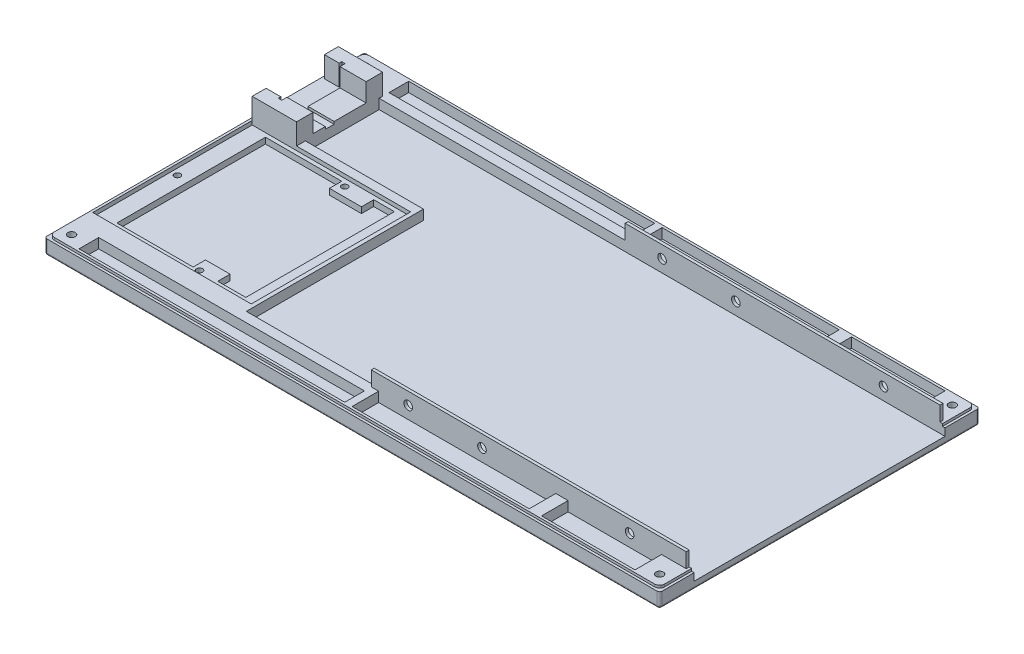
SolidWorks part; units mm, degrees
ref_plane "Front Plane" through (0, 0, 0) normal (0, 0, 1) x (1, 0, 0)
ref_plane "Top Plane" through (0, 0, 0) normal (0, 1, 0) x (1, 0, 0)
ref_plane "Right Plane" through (0, 0, 0) normal (1, 0, 0) x (0, 0, -1)
sketch "Sketch1" plane through (0, 0, 0) normal (0, 1, 0) x (1, 0, 0)
  line L1 (-125, -65) -> (125, -65)
  line L2 (-125, -65) -> (-125, 65)
  line L3 (-125, 65) -> (125, 65)
  line L4 (125, -65) -> (125, 65)
  line L5 (-125, -65) -> (125, 65) construction
  line L6 (-125, 65) -> (125, -65) construction
  point P0 (0, 0)
extrude "Boss-Extrude1" add sketch "Sketch1" along normal blind 3
sketch "Sketch2" plane through (0, 0, 0) normal (0, 1, 0) x (1, 0, 0)
  line L0 (125, -65) -> (125, 65) construction
  line L1 (-125, 65) -> (125, 65)
  line L2 (-125, 65) -> (-125, 64)
  line L3 (-125, 64) -> (125, 64)
  line L4 (125, 65) -> (125, 64)
  dimension "D1" = 1
extrude "Boss-Extrude2" add sketch "Sketch2" along normal blind 6
sketch "Sketch3" plane through (0, 3, 0) normal (0, 1, 0) x (1, 0, 0)
  line L0 (125, -65) -> (125, 64) construction
  line L1 (-125, -65) -> (125, -65)
  line L2 (-125, -65) -> (-125, -64)
  line L3 (-125, -64) -> (125, -64)
  line L4 (125, -65) -> (125, -64)
  dimension "D1" = 1
extrude "Boss-Extrude3" add sketch "Sketch3" along normal blind 3
sketch "Sketch4" plane through (0, 3, 0) normal (0, 1, 0) x (1, 0, 0)
  line L0 (125, -64) -> (-125, -64) construction
  line L1 (-125, 64) -> (-124, 64)
  line L2 (-125, 64) -> (-125, -64)
  line L3 (-125, -64) -> (-124, -64)
  line L4 (-124, 64) -> (-124, -64)
  dimension "D1" = 1
extrude "Boss-Extrude4" add sketch "Sketch4" along normal blind 3
sketch "Sketch6" plane through (0, 3, 0) normal (0, 1, 0) x (1, 0, 0)
  line L1 (125, -65) -> (124, -65)
  line L2 (125, -65) -> (125, -51)
  line L3 (125, -51) -> (124, -51)
  line L4 (124, -65) -> (124, -51)
  dimension "D1" = 1
  dimension "D2" = 14
extrude "Boss-Extrude5" add sketch "Sketch6" along normal blind 3
sketch "Sketch7" plane through (0, 3, 0) normal (0, 1, 0) x (1, 0, 0)
  line L1 (125, 65) -> (124, 65)
  line L2 (125, 65) -> (125, 51)
  line L3 (125, 51) -> (124, 51)
  line L4 (124, 65) -> (124, 51)
  dimension "D1" = 1
  dimension "D2" = 14
extrude "Boss-Extrude6" add sketch "Sketch7" along normal blind 3
sketch "Sketch8" plane through (0, 3, 0) normal (0, 1, 0) x (1, 0, 0)
  line L0 (-124, 64) -> (124, 64) construction
  line L1 (124, 51) -> (123, 51)
  line L2 (124, 51) -> (124, 64)
  line L3 (124, 64) -> (123, 64)
  line L4 (123, 51) -> (123, 64)
  dimension "D1" = 1
extrude "Boss-Extrude7" add sketch "Sketch8" along normal blind 4
sketch "Sketch10" plane through (0, 3, 0) normal (0, 1, 0) x (1, 0, 0)
  line L0 (-124, -64) -> (-124, 64) construction
  line L1 (123, 64) -> (-124, 64)
  line L2 (123, 64) -> (123, 63)
  line L3 (123, 63) -> (-124, 63)
  line L4 (-124, 64) -> (-124, 63)
  dimension "D1" = 1
extrude "Boss-Extrude8" add sketch "Sketch10" along normal blind 4
sketch "Sketch11" plane through (0, 3, 0) normal (0, 1, 0) x (1, 0, 0)
  line L0 (124, -64) -> (-124, -64) construction
  line L1 (-124, 63) -> (-123, 63)
  line L2 (-124, 63) -> (-124, -64)
  line L3 (-124, -64) -> (-123, -64)
  line L4 (-123, 63) -> (-123, -64)
  dimension "D1" = 1
extrude "Boss-Extrude9" add sketch "Sketch11" along normal blind 4
sketch "Sketch14" plane through (0, 3, 0) normal (0, 1, 0) x (1, 0, 0)
  line L0 (124, -51) -> (124, -64) construction
  line L1 (-123, -64) -> (124, -64)
  line L2 (-123, -64) -> (-123, -63)
  line L3 (-123, -63) -> (124, -63)
  line L4 (124, -64) -> (124, -63)
  dimension "D1" = 1
extrude "Boss-Extrude10" add sketch "Sketch14" along normal blind 4
sketch "Sketch15" plane through (0, 3, 0) normal (0, 1, 0) x (1, 0, 0)
  line L1 (124, -63) -> (123, -63)
  line L2 (124, -63) -> (124, -51)
  line L3 (124, -51) -> (123, -51)
  line L4 (123, -63) -> (123, -51)
  dimension "D1" = 1
extrude "Boss-Extrude11" add sketch "Sketch15" along normal blind 4
fillet "Fillet1" radius 1 8 edges at (0, 0, -65) (-125, 3, -65) (-125, 0, 0) (-125, 3, 65) (125, 3, -65) (125, 3, 65) (0, 0, 65) (125, 0, 0)
sketch "Sketch17" plane through (0, 3, 0) normal (0, 1, 0) x (1, 0, 0)
  line L1 (123, 51) -> (-5, 51)
  line L2 (123, 51) -> (123, 52.2)
  line L3 (123, 52.2) -> (-5, 52.2)
  line L4 (-5, 51) -> (-5, 52.2)
  dimension "D1" = 1.2
  dimension "D2" = 128
extrude "Boss-Extrude12" add sketch "Sketch17" along normal blind 10
sketch "Sketch19" plane through (0, 3, 0) normal (0, 1, 0) x (1, 0, 0)
  line L1 (123, -51) -> (-5, -51)
  line L2 (123, -51) -> (123, -52.2)
  line L3 (123, -52.2) -> (-5, -52.2)
  line L4 (-5, -51) -> (-5, -52.2)
  dimension "D1" = 1.2
  dimension "D2" = 128
extrude "Boss-Extrude13" add sketch "Sketch19" along normal blind 10
sketch "Sketch22" plane through (0, 3, 0) normal (0, 1, 0) x (1, 0, 0)
  line L0 (123, -63) -> (-123, -63) construction
  line L1 (-5, -52.2) -> (-2, -52.2)
  line L2 (-5, -52.2) -> (-5, -63)
  line L3 (-5, -63) -> (-2, -63)
  line L4 (-2, -52.2) -> (-2, -63)
  dimension "D1" = 3
extrude "Boss-Extrude14" add sketch "Sketch22" along normal blind 4
sketch "Sketch24" plane through (0, 3, 0) normal (0, 1, 0) x (1, 0, 0)
  line L0 (-123, 63) -> (123, 63) construction
  line L1 (-5, 52.2) -> (-2, 52.2)
  line L2 (-5, 52.2) -> (-5, 63)
  line L3 (-5, 63) -> (-2, 63)
  line L4 (-2, 52.2) -> (-2, 63)
  dimension "D1" = 3
extrude "Boss-Extrude15" add sketch "Sketch24" along normal blind 4
sketch "Sketch25" plane through (0, 0, -51) normal (0, 0, 1) x (1, 0, 0)
  circle A0 centre (100, 8) radius 1.75
  dimension "D1" = 5
  dimension "D2" = 25
extrude "FloppyMountHole001" cut sketch "Sketch25" against normal up to next
sketch "Sketch26" plane through (0, 0, -51) normal (0, 0, 1) x (1, 0, 0)
  line L0 (-5, 13) -> (123, 13) construction
  circle A0 centre (40, 8) radius 1.75
  dimension "D1" = 5
  dimension "D2" = 85
extrude "FloppyMountHole002" cut sketch "Sketch26" against normal up to next
sketch "Sketch27" plane through (0, 0, -51) normal (0, 0, 1) x (1, 0, 0)
  circle A0 centre (10, 8) radius 1.75
  dimension "D1" = 115
  dimension "D2" = 5
extrude "FloppyMountHole003" cut sketch "Sketch27" against normal up to next
sketch "Sketch28" plane through (0, 0, 52.2) normal (0, 0, 1) x (1, 0, 0)
  circle A0 centre (100, 8) radius 1.75
  dimension "D1" = 5
  dimension "D2" = 25
extrude "FloppyMountHole004" cut sketch "Sketch28" against normal up to next
sketch "Sketch29" plane through (0, 0, 52.2) normal (0, 0, 1) x (1, 0, 0)
  circle A0 centre (40, 8) radius 1.75
  dimension "D1" = 5
  dimension "D2" = 85
extrude "FloppyMountHole005" cut sketch "Sketch29" against normal up to next
sketch "Sketch30" plane through (0, 0, 52.2) normal (0, 0, 1) x (1, 0, 0)
  circle A0 centre (10, 8) radius 1.75
  dimension "D1" = 5
  dimension "D2" = 115
extrude "FloppyMountHole006" cut sketch "Sketch30" against normal up to next
sketch "Sketch31" plane through (0, 3, 0) normal (0, 1, 0) x (1, 0, 0)
  line L0 (123, -63) -> (-2, -63) construction
  line L1 (75, -63) -> (70, -63)
  line L2 (75, -63) -> (75, -52.2)
  line L3 (75, -52.2) -> (70, -52.2)
  line L4 (70, -63) -> (70, -52.2)
  line L5 (-5, -52.2) -> (123, -52.2) construction
  dimension "D1" = 5
  dimension "D2" = 48
extrude "Boss-Extrude16" add sketch "Sketch31" along normal blind 4
sketch "Sketch33" plane through (0, 3, 0) normal (0, 1, 0) x (1, 0, 0)
  line L0 (-2, 63) -> (123, 63) construction
  line L1 (75, 63) -> (70, 63)
  line L2 (75, 63) -> (75, 52.2)
  line L3 (75, 52.2) -> (70, 52.2)
  line L4 (70, 63) -> (70, 52.2)
  line L5 (123, 52.2) -> (-2, 52.2) construction
  dimension "D1" = 5
  dimension "D2" = 48
extrude "Boss-Extrude18" add sketch "Sketch33" along normal blind 4
fillet "Fillet2" radius 2 4 edges at (-124, 6.5, -64) (-124, 6.5, 64) (124, 6.5, 64) (124, 6.5, -64)
sketch "Sketch35" plane through (0, 3, 0) normal (0, 1, 0) x (1, 0, 0)
  line L0 (-123, -63) -> (-123, 63) construction
  line L1 (-57, -51) -> (-123, -51)
  line L2 (-57, -51) -> (-57, -47.4)
  line L3 (-57, -47.4) -> (-123, -47.4)
  line L4 (-123, -51) -> (-123, -47.4)
  dimension "D1" = 66
  dimension "D2" = 3.6
extrude "GWOuter001" add sketch "Sketch35" along normal blind 4
sketch "Sketch36" plane through (0, 3, 0) normal (0, 1, 0) x (1, 0, 0)
  line L1 (-57, -47.4) -> (-58.6, -47.4)
  line L2 (-57, -47.4) -> (-57, 17.4)
  line L3 (-57, 17.4) -> (-58.6, 17.4)
  line L4 (-58.6, -47.4) -> (-58.6, 17.4)
  dimension "D1" = 1.6
  dimension "D2" = 64.8
extrude "GWOuter002" add sketch "Sketch36" along normal blind 4
sketch "Sketch37" plane through (0, 3, 0) normal (0, 1, 0) x (1, 0, 0)
  line L0 (-123, -47.4) -> (-123, 63) construction
  line L1 (-57, 17.4) -> (-123, 17.4)
  line L2 (-57, 17.4) -> (-57, 21)
  line L3 (-57, 21) -> (-123, 21)
  line L4 (-123, 17.4) -> (-123, 21)
  dimension "D1" = 3.6
extrude "GWOuter003" add sketch "Sketch37" along normal blind 4
sketch "Sketch38" plane through (0, 3, 0) normal (0, 1, 0) x (1, 0, 0)
  line L0 (-58.6, -47.4) -> (-123, -47.4) construction
  line L1 (-123, 17.4) -> (-116, 17.4)
  line L2 (-123, 17.4) -> (-123, -47.4)
  line L3 (-123, -47.4) -> (-116, -47.4)
  line L4 (-116, 17.4) -> (-116, -47.4)
  dimension "D1" = 7
extrude "GWSupportBack" add sketch "Sketch38" along normal blind 2.4
sketch "Sketch39" plane through (0, 3, 0) normal (0, 1, 0) x (1, 0, 0)
  line L0 (-58.6, -47.4) -> (-116, -47.4) construction
  line L1 (-58.6, 17.4) -> (-63.6, 17.4)
  line L2 (-58.6, 17.4) -> (-58.6, -47.4)
  line L3 (-58.6, -47.4) -> (-63.6, -47.4)
  line L4 (-63.6, 17.4) -> (-63.6, -47.4)
  dimension "D1" = 5
extrude "GWSupportFrt" add sketch "Sketch39" along normal blind 2.4
sketch "Sketch40" plane through (0, 3, 0) normal (0, 1, 0) x (1, 0, 0)
  line L0 (-63.6, 17.4) -> (-63.6, -47.4) construction
  line L1 (-116, 17.4) -> (-63.6, 17.4)
  line L2 (-116, 17.4) -> (-116, 15.8)
  line L3 (-116, 15.8) -> (-63.6, 15.8)
  line L4 (-63.6, 17.4) -> (-63.6, 15.8)
  dimension "D1" = 1.6
extrude "GWSupportLt" add sketch "Sketch40" along normal blind 2.4
sketch "Sketch41" plane through (0, 3, 0) normal (0, 1, 0) x (1, 0, 0)
  line L0 (-63.6, 15.8) -> (-63.6, -47.4) construction
  line L1 (-116, -47.4) -> (-63.6, -47.4)
  line L2 (-116, -47.4) -> (-116, -44.6)
  line L3 (-116, -44.6) -> (-63.6, -44.6)
  line L4 (-63.6, -47.4) -> (-63.6, -44.6)
  dimension "D1" = 2.8
extrude "GWSupportRt" add sketch "Sketch41" along normal blind 2.4
sketch "Sketch43" plane through (0, 3, 0) normal (0, 1, 0) x (1, 0, 0)
  line L0 (-63.6, -44.6) -> (-116, -44.6) construction
  line L1 (-75, -39.6) -> (-85, -39.6)
  line L2 (-75, -39.6) -> (-75, -44.6)
  line L3 (-75, -44.6) -> (-85, -44.6)
  line L4 (-85, -39.6) -> (-85, -44.6)
  dimension "D1" = 11.4
  dimension "D2" = 10
  dimension "D3" = 5
extrude "GWScrewRt" add sketch "Sketch43" along normal blind 2.4
sketch "Sketch44" plane through (0, 3, 0) normal (0, 1, 0) x (1, 0, 0)
  line L0 (-123, -63) -> (-123, -51) construction
  line L1 (-5, -51) -> (-123, -51)
  line L2 (-5, -51) -> (-5, -55)
  line L3 (-5, -55) -> (-123, -55)
  line L4 (-123, -51) -> (-123, -55)
  dimension "D1" = 4
extrude "Boss-Extrude28" add sketch "Sketch44" along normal blind 4
sketch "Sketch45" plane through (0, 3, 0) normal (0, 1, 0) x (1, 0, 0)
  line L0 (-57, 21) -> (-123, 21) construction
  line L1 (-123, 63) -> (-105, 63)
  line L2 (-123, 63) -> (-123, 21)
  line L3 (-123, 21) -> (-105, 21)
  line L4 (-105, 63) -> (-105, 21)
  line L5 (-125, 64) -> (-125, -64) construction
  dimension "D1" = 20
extrude "Boss-Extrude29" add sketch "Sketch45" along normal blind 4
sketch "Sketch46" plane through (0, 3, 0) normal (0, 1, 0) x (1, 0, 0)
  line L0 (-5, -63) -> (-123, -63) construction
  line L1 (-123, -55) -> (-113, -55)
  line L2 (-123, -55) -> (-123, -63)
  line L3 (-123, -63) -> (-113, -63)
  line L4 (-113, -55) -> (-113, -63)
  dimension "D1" = 10
extrude "Boss-Extrude30" add sketch "Sketch46" along normal blind 4
sketch "Sketch47" plane through (0, 3, 0) normal (0, 1, 0) x (1, 0, 0)
  line L0 (123, 52.2) -> (75, 52.2) construction
  line L1 (123, 63) -> (113, 63)
  line L2 (123, 63) -> (123, 52.2)
  line L3 (123, 52.2) -> (113, 52.2)
  line L4 (113, 63) -> (113, 52.2)
  dimension "D1" = 10
extrude "Boss-Extrude31" add sketch "Sketch47" along normal blind 4
sketch "Sketch48" plane through (0, 3, 0) normal (0, 1, 0) x (1, 0, 0)
  line L0 (75, -52.2) -> (123, -52.2) construction
  line L1 (123, -63) -> (113, -63)
  line L2 (123, -63) -> (123, -52.2)
  line L3 (123, -52.2) -> (113, -52.2)
  line L4 (113, -63) -> (113, -52.2)
  dimension "D1" = 10
extrude "Boss-Extrude32" add sketch "Sketch48" along normal blind 4
sketch "Sketch49" plane through (0, 3, 0) normal (0, 1, 0) x (1, 0, 0)
  line L0 (-105, 21) -> (-105, 63) construction
  line L1 (-5, 51) -> (-105, 51)
  line L2 (-5, 51) -> (-5, 55)
  line L3 (-5, 55) -> (-105, 55)
  line L4 (-105, 51) -> (-105, 55)
  dimension "D1" = 4
extrude "Boss-Extrude33" add sketch "Sketch49" along normal blind 4
sketch "Sketch50" plane through (0, 3, 0) normal (0, 1, 0) x (1, 0, 0)
  line L0 (-116, 15.8) -> (-63.6, 15.8) construction
  line L2 (-72, 15.8) -> (-85, 15.8)
  line L3 (-72, 15.8) -> (-72, 10.8)
  line L4 (-72, 10.8) -> (-85, 10.8)
  line L5 (-85, 15.8) -> (-85, 10.8)
  dimension "D1" = 8.4
  dimension "D2" = 13
  dimension "D3" = 5
extrude "GWScrewLt" add sketch "Sketch50" along normal blind 2.4
sketch "Sketch51" plane through (0, 5.4, 0) normal (0, 1, 0) x (1, 0, 0)
  circle A0 centre (-82.5, 14.5) radius 1.25
  dimension "D1" = 40.5
  dimension "D2" = 2.9
extrude "GWLSideMountHole" cut sketch "Sketch51" against normal offset from surface (5 mm away) 5
sketch "Sketch52" plane through (0, 5.4, 0) normal (0, 1, 0) x (1, 0, 0)
  line L0 (-123, 17.4) -> (-123, -47.4) construction
  circle A0 centre (-82.5, -44.5) radius 1.25
  dimension "D1" = 40.5
  dimension "D2" = 2.9
extrude "GWRSideMountHole" cut sketch "Sketch52" against normal offset from surface (5 mm away) 5
sketch "Sketch53" plane through (0, 5.4, 0) normal (0, 1, 0) x (1, 0, 0)
  circle A0 centre (-120.5, -15.5) radius 1.25
  dimension "D1" = 31.9
  dimension "D2" = 2.5
extrude "GWBackMountHole" cut sketch "Sketch53" against normal offset from surface (5 mm away) 5
sketch "Sketch54" plane through (0, 7, 0) normal (0, 1, 0) x (1, 0, 0)
  line L6 (-123, 17.4) -> (-117, 17.4)
  line L7 (-123, 17.4) -> (-123, 23.05)
  line L8 (-123, 23.05) -> (-117, 23.05)
  line L9 (-117, 17.4) -> (-117, 23.05)
  dimension "D1" = 5.65
  dimension "D2" = 6
extrude "Molex001" add sketch "Sketch54" along normal blind 8.5
sketch "Sketch55" plane through (0, 7, 0) normal (0, 1, 0) x (1, 0, 0)
  line L1 (-123, 52.4) -> (-117, 52.4)
  line L2 (-123, 52.4) -> (-123, 46.75)
  line L3 (-123, 46.75) -> (-117, 46.75)
  line L4 (-117, 52.4) -> (-117, 46.75)
  line L5 (-125, 64) -> (-125, -64) construction
  dimension "D1" = 23.7
  dimension "D2" = 5.65
  dimension "D3" = 8
  dimension "D4" = 2
extrude "Molex002" add sketch "Sketch55" along normal blind 8.5
sketch "Sketch56" plane through (0, 7, 0) normal (0, 1, 0) x (1, 0, 0)
  line L5 (-117, 17.4) -> (-115.6, 17.4)
  line L6 (-117, 17.4) -> (-117, 22)
  line L7 (-117, 22) -> (-115.6, 22)
  line L8 (-115.6, 17.4) -> (-115.6, 22)
  dimension "D1" = 4.6
  dimension "D2" = 1.4
extrude "Molex003" add sketch "Sketch56" along normal blind 8.5
sketch "Sketch57" plane through (0, 7, 0) normal (0, 1, 0) x (1, 0, 0)
  line L1 (-117, 52.4) -> (-115.6, 52.4)
  line L2 (-117, 52.4) -> (-117, 47.8)
  line L3 (-117, 47.8) -> (-115.6, 47.8)
  line L4 (-115.6, 52.4) -> (-115.6, 47.8)
  dimension "D1" = 1.4
  dimension "D2" = 4.6
extrude "Molex004" add sketch "Sketch57" along normal blind 8.5
sketch "Sketch58" plane through (0, 7, 0) normal (0, 1, 0) x (1, 0, 0)
  line L0 (-105, 21) -> (-105, 51) construction
  line L1 (-115.6, 52.4) -> (-105, 52.4)
  line L2 (-115.6, 52.4) -> (-115.6, 45.7)
  line L3 (-115.6, 45.7) -> (-105, 45.7)
  line L4 (-105, 52.4) -> (-105, 45.7)
  dimension "D1" = 6.7
extrude "Molex005" add sketch "Sketch58" along normal blind 8.5
sketch "Sketch59" plane through (0, 7, 0) normal (0, 1, 0) x (1, 0, 0)
  line L0 (-105, 21) -> (-105, 45.7) construction
  line L1 (-115.6, 17.4) -> (-105, 17.4)
  line L2 (-115.6, 17.4) -> (-115.6, 24.1)
  line L3 (-115.6, 24.1) -> (-105, 24.1)
  line L4 (-105, 17.4) -> (-105, 24.1)
  dimension "D1" = 6.7
extrude "Molex006" add sketch "Sketch59" along normal blind 8.5
sketch "Sketch60" plane through (0, 7, 0) normal (0, 1, 0) x (1, 0, 0)
  line L0 (-105, 24.1) -> (-105, 45.7) construction
  line L1 (-115.6, 45.7) -> (-105, 45.7)
  line L2 (-115.6, 45.7) -> (-115.6, 32.7)
  line L3 (-115.6, 32.7) -> (-105, 32.7)
  line L4 (-105, 45.7) -> (-105, 32.7)
  dimension "D1" = 13
extrude "Molex007" add sketch "Sketch60" along normal blind 1
sketch "Sketch61" plane through (0, 7, 0) normal (0, 1, 0) x (1, 0, 0)
  line L0 (-105, 24.1) -> (-105, 32.7) construction
  line L1 (-115.6, 24.1) -> (-105, 24.1)
  line L2 (-115.6, 24.1) -> (-115.6, 29.1)
  line L3 (-115.6, 29.1) -> (-105, 29.1)
  line L4 (-105, 24.1) -> (-105, 29.1)
  dimension "D1" = 5
extrude "Molex008" add sketch "Sketch61" along normal blind 1
sketch "Sketch62" plane through (0, 7, 0) normal (0, 1, 0) x (1, 0, 0)
  line L0 (124, 65) -> (-124, 65) construction
  line L1 (-125, 64) -> (-125, -64) construction
  circle A0 centre (-119.5, 59.5) radius 1.5
  dimension "D1" = 5.5
  dimension "D2" = 5.5
extrude "CaseMuntHole001" cut sketch "Sketch62" against normal through all
sketch "Sketch63" plane through (0, 7, 0) normal (0, 1, 0) x (1, 0, 0)
  line L0 (125, 51) -> (125, 64) construction
  line L1 (124, 65) -> (-124, 65) construction
  circle A0 centre (119.5, 59.5) radius 1.5
  dimension "D1" = 5.5
  dimension "D2" = 5.5
extrude "CaseMuntHole002" cut sketch "Sketch63" against normal through all
sketch "Sketch64" plane through (0, 7, 0) normal (0, 1, 0) x (1, 0, 0)
  line L0 (125, -64) -> (125, -51) construction
  line L1 (-124, -65) -> (124, -65) construction
  circle A0 centre (119.5, -59.5) radius 1.5
  dimension "D1" = 5.5
  dimension "D2" = 5.5
extrude "CaseMuntHole003" cut sketch "Sketch64" against normal through all
sketch "Sketch65" plane through (0, 7, 0) normal (0, 1, 0) x (1, 0, 0)
  line L0 (-124, -65) -> (124, -65) construction
  line L1 (-125, 64) -> (-125, -64) construction
  circle A0 centre (-119.5, -59.5) radius 1.5
  dimension "D1" = 5.5
  dimension "D2" = 5.5
extrude "CaseMuntHole004" cut sketch "Sketch65" against normal through all
chamfer "CaseMountHoleCountersink" distance 2 4 edges at (-119.5, 0, -58) (119.5, 0, -58) (119.5, 0, 61) (-119.5, 0, 61)
